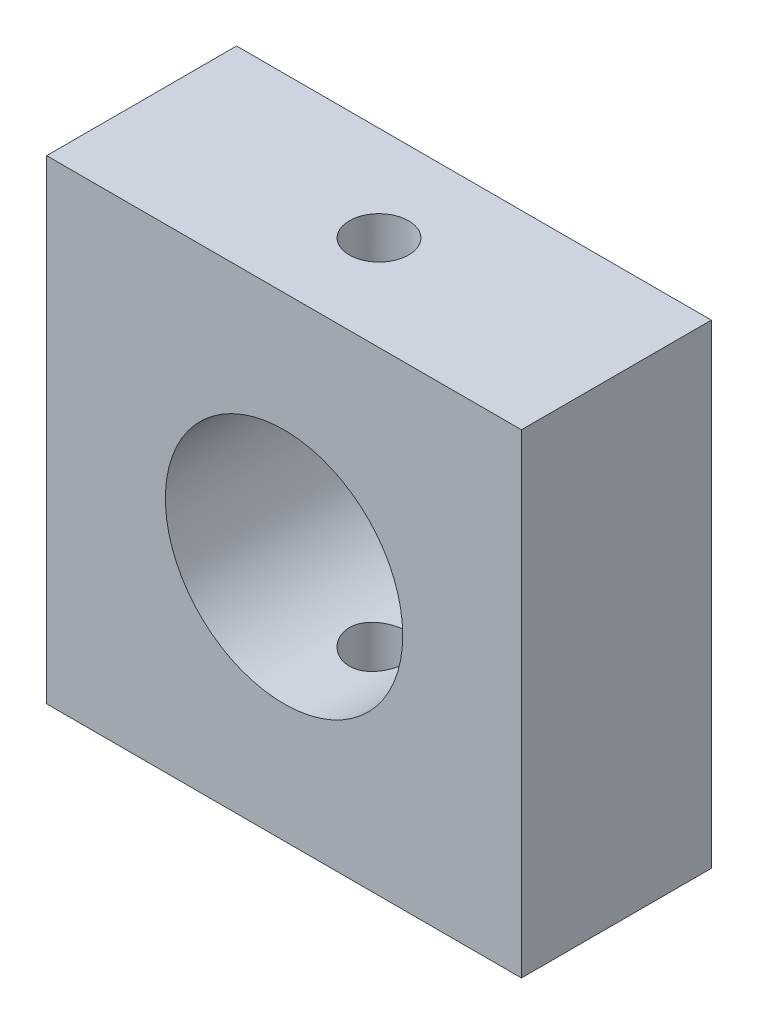
SolidWorks part; units mm, degrees
ref_plane "Front Plane" through (0, 0, 0) normal (0, 0, 1) x (1, 0, 0)
ref_plane "Top Plane" through (0, 0, 0) normal (0, 1, 0) x (1, 0, 0)
ref_plane "Right Plane" through (0, 0, 0) normal (1, 0, 0) x (0, 0, -1)
sketch "Sketch1" plane through (0, 0, 0) normal (0, 0, 1) x (1, 0, 0)
  line L0 (50, -10) -> (50, -90) construction
  line L4 (40, -40) -> (60, -40)
  line L5 (40, -40) -> (40, -60)
  line L6 (40, -60) -> (60, -60)
  line L7 (60, -40) -> (60, -60)
  line L8 (40, -40) -> (60, -60) construction
  line L9 (40, -60) -> (60, -40) construction
  circle A0 centre (50, -50) radius 5
extrude "Boss-Extrude1" add sketch "Sketch1" along normal blind 8
sketch "Sketch3" plane through (0, -60, 0) normal (0, -1, 0) x (-1, 0, 0)
  line L0 (-40, -4) -> (-60, -4) construction
  line L1 (-40, -8) -> (-40, 0) construction
  line L2 (-60, -8) -> (-60, 0) construction
  circle A0 centre (-50, -4) radius 1.25
extrude "Cut-Extrude1" cut sketch "Sketch3" against normal blind 20
